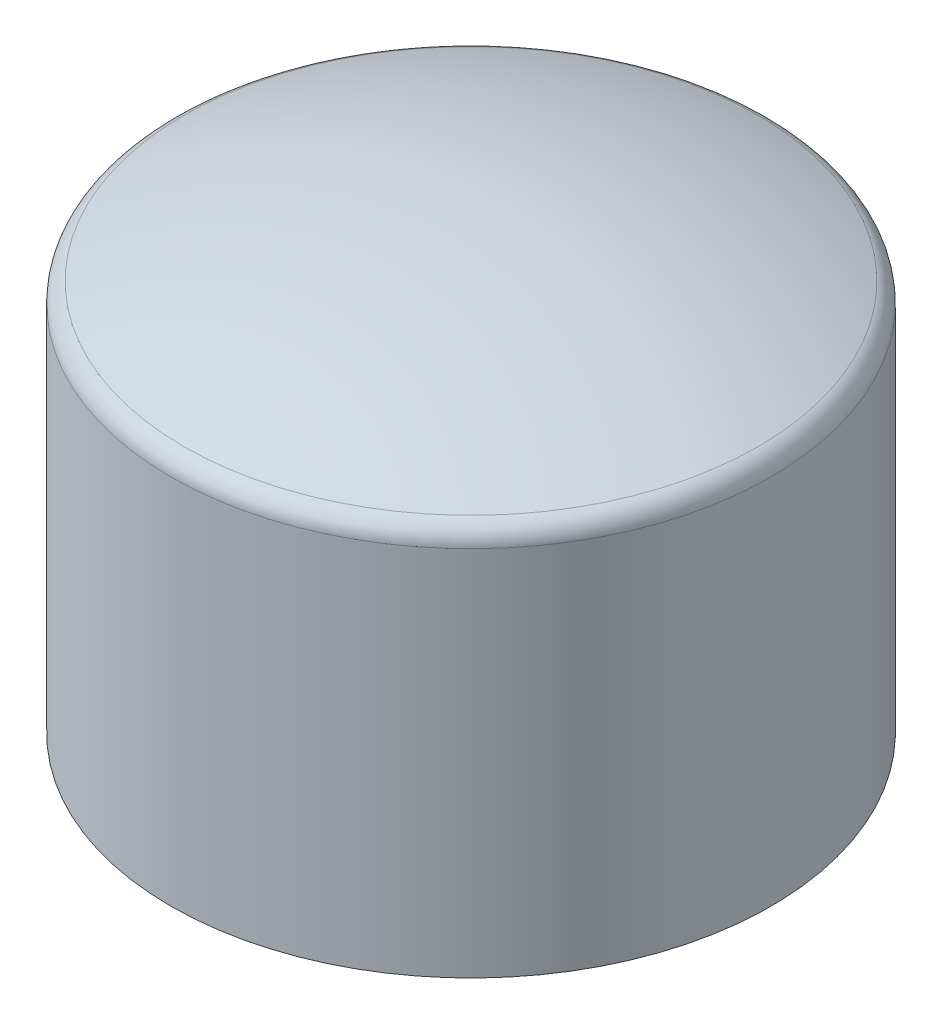
SolidWorks part; units mm, degrees
ref_plane "Front Plane" through (0, 0, 0) normal (0, 0, 1) x (1, 0, 0)
ref_plane "Top Plane" through (0, 0, 0) normal (0, 1, 0) x (1, 0, 0)
ref_plane "Right Plane" through (0, 0, 0) normal (1, 0, 0) x (0, 0, -1)
sketch "Sketch2" plane through (0, 0, 0) normal (1, 0, 0) x (0, 0, -1)
  line L0 (0, 0) -> (0, 10.5) construction
  line L1 (0, 0) -> (7, 0)
  line L2 (7, 0) -> (7, 9)
  line L3 (0, 10.5) -> (-4.7056, 10.5) construction
  line L4 (0, 0) -> (0, 10.5)
  arc A0 (0, 10.5) -> (7, 9) centre (0, -6.5833) cw
  dimension "D3" = 10.5
  dimension "D1" = 7
  dimension "D2" = 9
revolve "Revolve1" add sketch "Sketch2" angle 360 about L4
fillet "Fillet1" radius 0.5 1 edges at (0, 9, -7)
